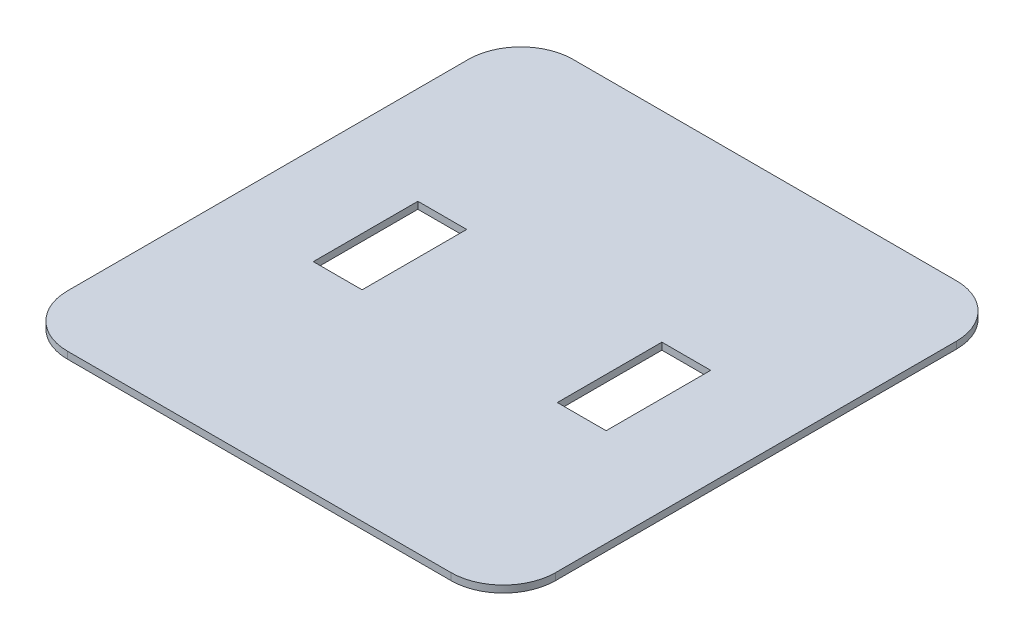
SolidWorks part; units mm, degrees
ref_plane "Face" through (0, 0, 0) normal (0, 0, 1) x (1, 0, 0)
ref_plane "Dessus" through (0, 0, 0) normal (0, 1, 0) x (1, 0, 0)
ref_plane "Droite" through (0, 0, 0) normal (1, 0, 0) x (0, 0, -1)
sketch "Esquisse1" plane through (0, 0, 0) normal (0, 1, 0) x (1, 0, 0)
  line L0 (0, 0) -> (0, -290) construction
  line L1 (110, 0) -> (-110, 0)
  line L2 (-70, 0) -> (-70, -290) construction
  line L3 (-140, -30) -> (-140, -260)
  line L4 (84, -115) -> (56, -115)
  line L5 (-110, -290) -> (110, -290)
  line L6 (-84, -175) -> (-56, -175)
  line L7 (0, -145) -> (-140, -145) construction
  line L8 (140, -30) -> (140, -260)
  line L9 (-84, -175) -> (-84, -115)
  line L10 (-84, -115) -> (-56, -115)
  line L11 (-56, -175) -> (-56, -115)
  line L12 (84, -175) -> (84, -115)
  line L13 (84, -175) -> (56, -175)
  line L14 (56, -175) -> (56, -115)
  arc A0 (-110, 0) -> (-140, -30) centre (-110, -30) ccw
  arc A1 (-140, -260) -> (-110, -290) centre (-110, -260) ccw
  arc A4 (140, -260) -> (110, -290) centre (110, -260) cw
  arc A5 (110, 0) -> (140, -30) centre (110, -30) cw
  dimension "D5" = 28
  dimension "D1" = 230
  dimension "D2" = 290
  dimension "D3" = 140
  dimension "D4" = 70
  dimension "D6" = 60
extrude "Extrusion1" add sketch "Esquisse1" along normal blind 4
